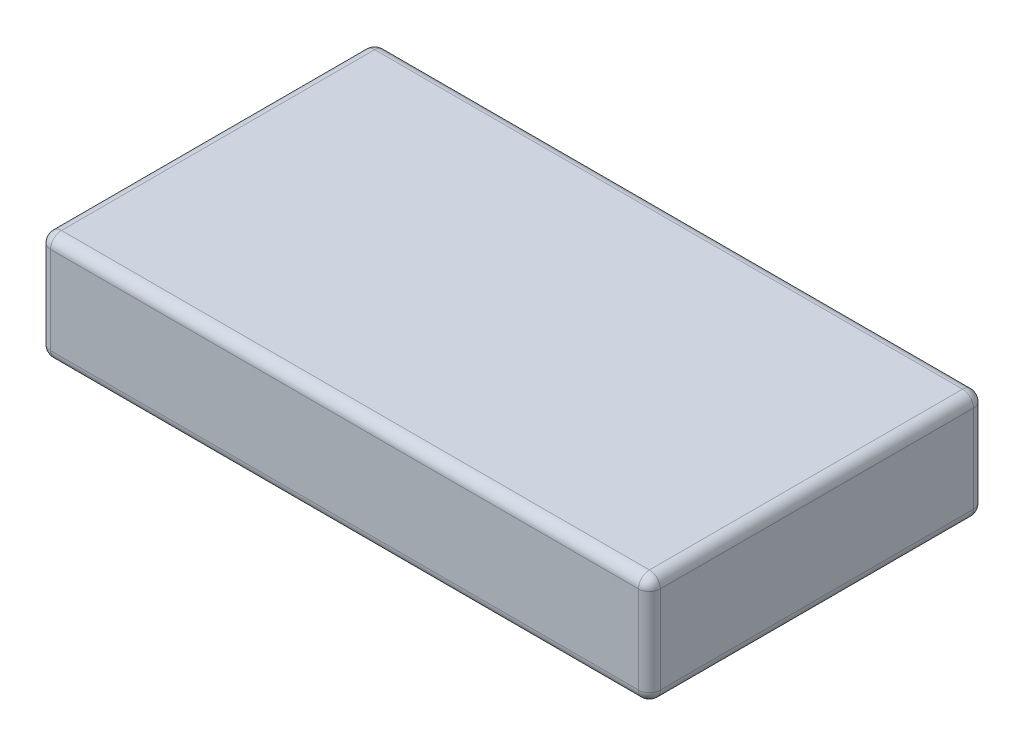
SolidWorks part; units mm, degrees
ref_plane "Front" through (0, 0, 0) normal (0, 0, 1) x (1, 0, 0)
ref_plane "Top" through (0, 0, 0) normal (0, 1, 0) x (1, 0, 0)
ref_plane "Right" through (0, 0, 0) normal (1, 0, 0) x (0, 0, -1)
sketch "Sketch1" plane through (0, 0, 0) normal (0, 1, 0) x (1, 0, 0)
  line L1 (0, 0) -> (55.7, 0)
  line L2 (0, 0) -> (0, 30.6)
  line L3 (0, 30.6) -> (55.7, 30.6)
  line L4 (55.7, 0) -> (55.7, 30.6)
  dimension "D1" = 55.7
  dimension "D2" = 30.6
extrude "Boss-Extrude1" add sketch "Sketch1" along normal blind 10
fillet "Fillet1" radius 1 12 edges at (55.7, 5, -30.6) (27.85, 10, -30.6) (27.85, 0, -30.6) (0, 5, -30.6) (0, 10, -15.3) (0, 0, -15.3) (0, 5, 0) (27.85, 10, 0) (55.7, 5, 0) (27.85, 0, 0) (55.7, 0, -15.3) (55.7, 10, -15.3)
